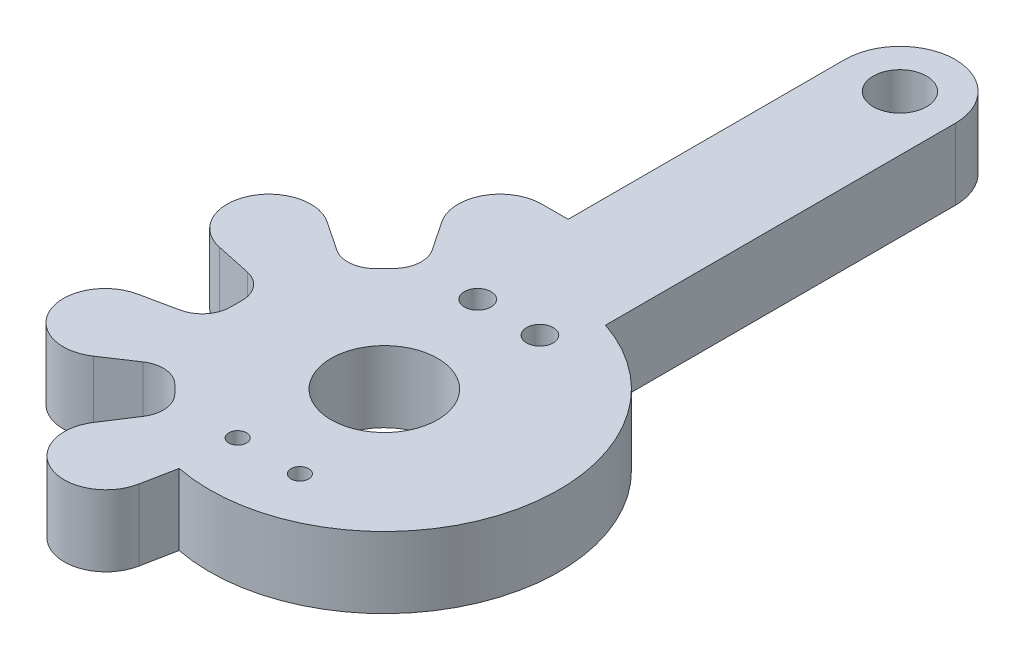
SolidWorks part; units mm, degrees
ref_plane "Alzado" through (0, 0, 0) normal (0, 0, 1) x (1, 0, 0)
ref_plane "Planta" through (0, 0, 0) normal (0, 1, 0) x (1, 0, 0)
ref_plane "Vista lateral" through (0, 0, 0) normal (1, 0, 0) x (0, 0, -1)
sketch "Croquis1" plane through (0, 0, 0) normal (0, 1, 0) x (1, 0, 0)
  line L0 (-2.7711, 3.7324) -> (-1.2957, 3.7324)
  line L1 (-1.2957, 3.7324) -> (-1.2957, 19.2963)
  line L2 (4.9143, 19.2963) -> (4.9143, -0.3743)
  line L3 (-3.6189, -1.5903) -> (-4.7282, 0.0653)
  line L4 (-3.7974, -3.5577) -> (-4.2934, -4.068)
  line L5 (-7.9555, -3.1633) -> (-6.2921, -4.2778)
  line L6 (-9.756, -7.4262) -> (-7.7561, -7.8503)
  line L7 (-6.5124, -9.3854) -> (-6.5124, -10.0335)
  line L8 (-9.7684, -12.0186) -> (-7.7788, -11.5967)
  line L9 (-7.9761, -16.2811) -> (-6.2998, -15.1657)
  line L10 (-0.4737, -21.2354) -> (-0.1005, -19.3404)
  line L11 (-4.743, -19.5049) -> (-3.6381, -17.8029)
  line L12 (-3.8447, -15.8387) -> (-4.3208, -15.3626)
  arc A0 (4.9143, 19.2963) -> (-1.2957, 19.2963) centre (1.8093, 19.2963) ccw
  circle A1 centre (1.8065, 19.2909) radius 1.4982
  arc A2 (-2.7711, 3.7324) -> (-4.7282, 0.0653) centre (-2.7711, 1.3766) ccw
  arc A3 (-7.9555, -3.1633) -> (-9.756, -7.4262) centre (-9.2672, -5.121) ccw
  arc A4 (-9.7684, -12.0186) -> (-7.9761, -16.2811) centre (-9.2801, -14.3213) ccw
  arc A5 (-4.743, -19.5049) -> (-0.4737, -21.2354) centre (-2.7753, -20.7822) ccw
  circle A7 centre (1.8061, -9.7044) radius 2.9962
  circle A8 centre (0.0593, -2.7087) radius 0.75
  circle A9 centre (3.5593, -2.7087) radius 0.75
  circle A10 centre (0.0593, -16.2087) radius 0.5
  circle A11 centre (3.5593, -16.2087) radius 0.5
  arc A12 (-4.3208, -15.3626) -> (-6.2998, -15.1657) centre (-5.4305, -16.4722) ccw
  arc A13 (-3.6381, -17.8029) -> (-3.8447, -15.8387) centre (-4.9543, -16.9484) ccw
  arc A14 (-7.7788, -11.5967) -> (-6.5124, -10.0335) centre (-8.1103, -10.0335) ccw
  arc A15 (-6.5124, -9.3854) -> (-7.7561, -7.8503) centre (-8.0817, -9.3854) ccw
  arc A16 (-6.2921, -4.2778) -> (-4.2934, -4.068) centre (-5.4186, -2.9741) ccw
  arc A17 (-3.7974, -3.5577) -> (-3.6189, -1.5903) centre (-4.9226, -2.4638) ccw
  arc A19 (-0.1005, -19.3404) -> (4.9143, -0.3743) centre (1.7934, -9.6951) ccw
  point P2 (0, 0)
  point P6 (0, 0)
  point P8 (0, 0)
  point P10 (0, 0)
  point P14 (0, 0)
  point P34 (0, 0)
  point P62 (0, 0)
  point P63 (0, 0)
  point P64 (0, 0)
  point P65 (0, 0)
  point P66 (0, 0)
  point P67 (0, 0)
  point P68 (0, 0)
  point P69 (0, 0)
  point P70 (0, 0)
  point P71 (0, 0)
  point P72 (0, 0)
  point P73 (0, 0)
  point P74 (0, 0)
  point P75 (0, 0)
  point P76 (0, 0)
extrude "Saliente-Extruir1" add sketch "Croquis1" along normal blind 4
